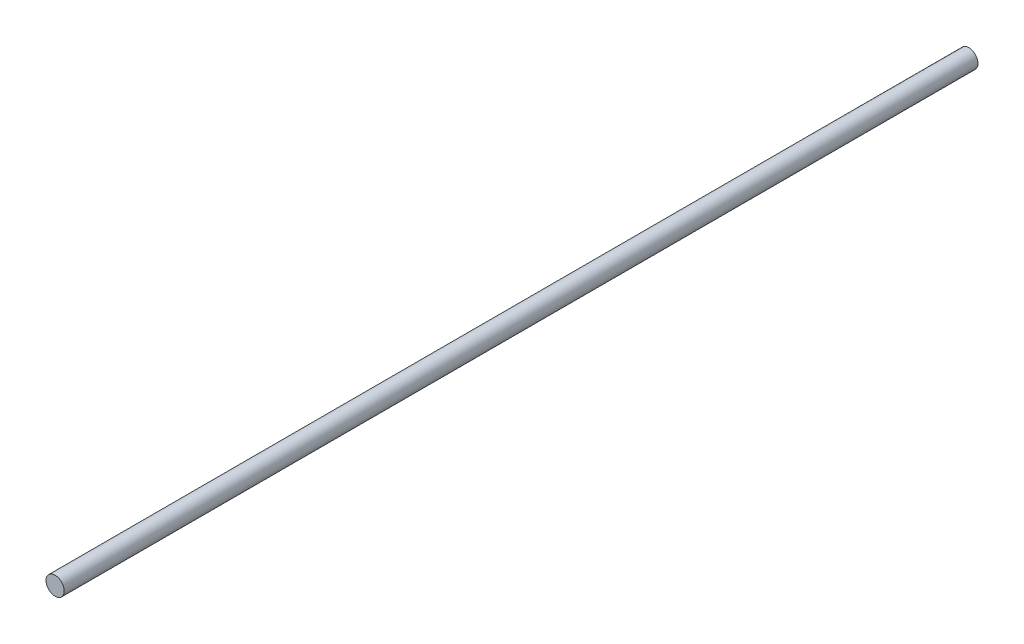
SolidWorks part; units mm, degrees
ref_plane "Piano frontale" through (0, 0, 0) normal (0, 0, 1) x (1, 0, 0)
ref_plane "Piano superiore" through (0, 0, 0) normal (0, 1, 0) x (1, 0, 0)
ref_plane "Piano destro" through (0, 0, 0) normal (1, 0, 0) x (0, 0, -1)
sketch "Schizzo1" plane through (0, 0, 0) normal (0, 0, 1) x (1, 0, 0)
  circle A0 centre (0, 0) radius 0.5
  dimension "D1" = 1
extrude "Estrusione-Estrusione1" add sketch "Schizzo1" along normal blind 50
